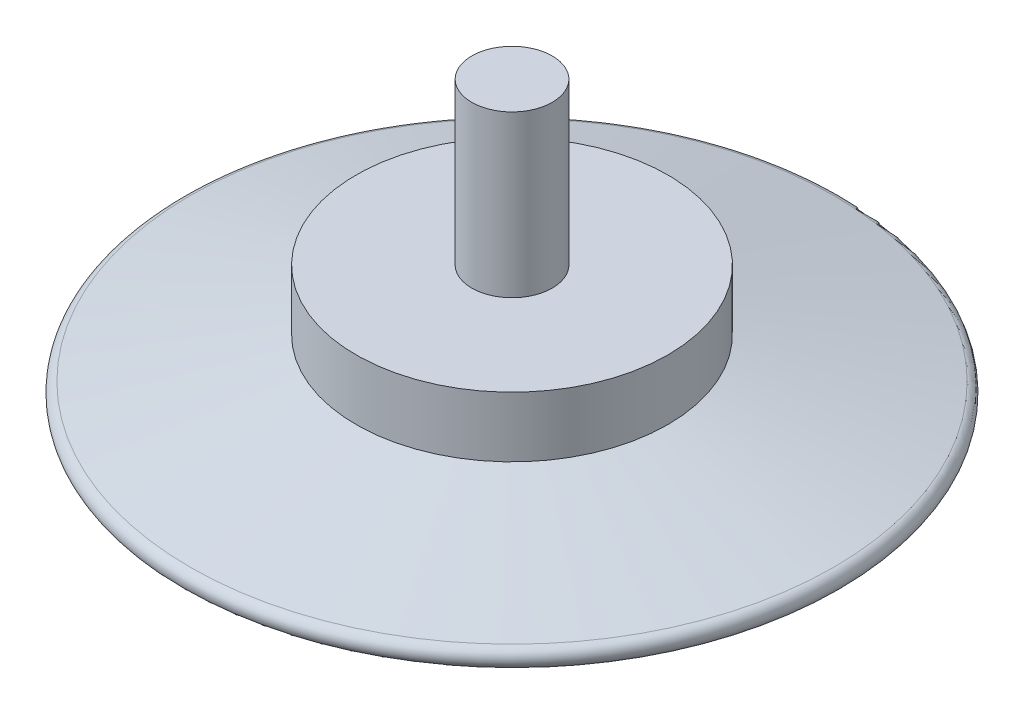
SolidWorks part; units mm, degrees
ref_plane "前视基准面" through (0, 0, 0) normal (0, 0, 1) x (1, 0, 0)
ref_plane "上视基准面" through (0, 0, 0) normal (0, 1, 0) x (1, 0, 0)
ref_plane "右视基准面" through (0, 0, 0) normal (1, 0, 0) x (0, 0, -1)
sketch "草图1" plane through (0, 0, 0) normal (0, 0, 1) x (1, 0, 0)
  line L0 (0, 0) -> (0, 14) construction
  line L1 (0, 14) -> (-2, 14)
  line L2 (-2, 14) -> (-2, 6)
  line L3 (-2, 6) -> (-7.75, 6)
  line L4 (-7.75, 6) -> (-7.75, 3)
  line L5 (-7.75, 3) -> (-16, 0.9857)
  line L6 (-15.8814, 0) -> (0, 0)
  line L7 (0, 0) -> (0, 14)
  arc A0 (-16, 0.9857) -> (-15.8814, 0) centre (-15.8814, 0.5) ccw
  dimension "D3" = 0.5
  dimension "D1" = 4
  dimension "D2" = 15.5
  dimension "D4" = 32
  dimension "D5" = 3
  dimension "D6" = 6
  dimension "D7" = 14
revolve "旋转1" add sketch "草图1" angle 360 about L0
cosmetic thread "装饰螺纹线1"
